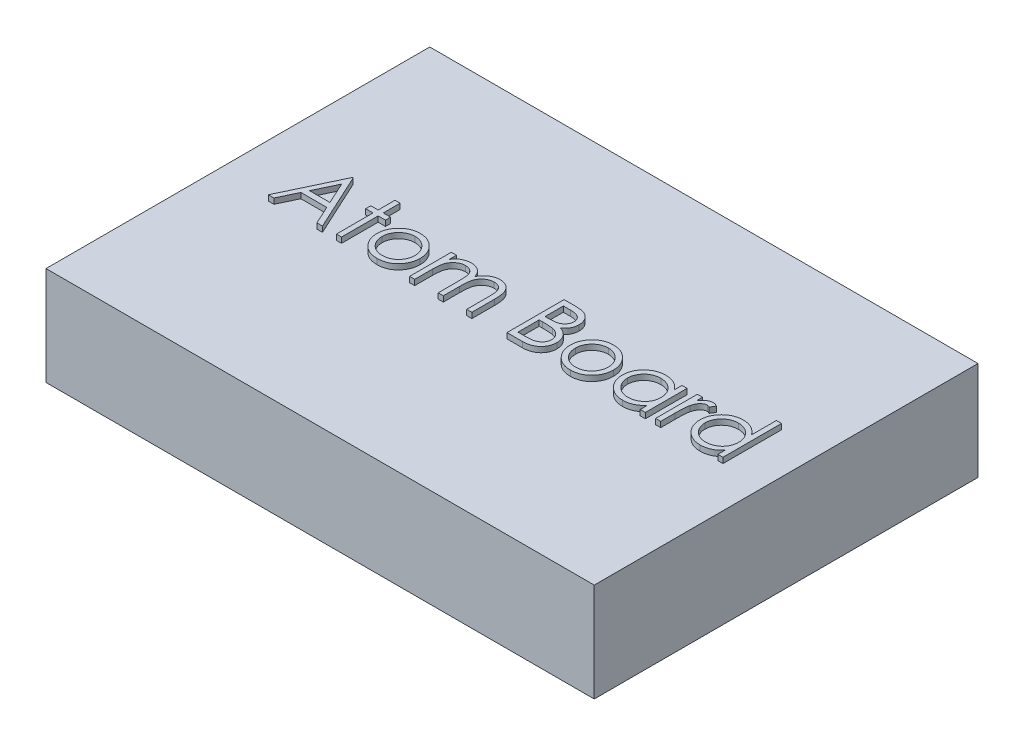
SolidWorks part; units mm, degrees
ref_plane "Front Plane" through (0, 0, 0) normal (0, 0, 1) x (1, 0, 0)
ref_plane "Top Plane" through (0, 0, 0) normal (0, 1, 0) x (1, 0, 0)
ref_plane "Right Plane" through (0, 0, 0) normal (1, 0, 0) x (0, 0, -1)
sketch "Sketch1" plane through (0, 0, 0) normal (0, 1, 0) x (1, 0, 0)
  line L1 (-127, -88.9) -> (127, -88.9)
  line L2 (-127, -88.9) -> (-127, 88.9)
  line L3 (-127, 88.9) -> (127, 88.9)
  line L4 (127, -88.9) -> (127, 88.9)
  line L5 (-127, -88.9) -> (127, 88.9) construction
  line L6 (-127, 88.9) -> (127, -88.9) construction
  point P0 (0, 0)
  dimension "D1" = 254
  dimension "D2" = 177.8
extrude "Boss-Extrude1" add sketch "Sketch1" along normal blind 45.72
sketch "Sketch2" plane through (0, 45.72, 0) normal (0, 1, 0) x (1, 0, 0)
  text T0 "Atom Board" font "Century Gothic" height in points 100
extrude "Boss-Extrude2" add sketch "Sketch2" along normal blind 2.54
sketch "Sketch3" plane through (0, 0, 0) normal (0, -1, 0) x (1, 0, 0)
  line L0 (0, 88.9) -> (0, -88.9) construction
  line L1 (-127, 88.9) -> (127, 88.9) construction
  line L2 (127, -88.9) -> (-127, -88.9) construction
  line L3 (127, 0) -> (-127, 0) construction
  line L4 (127, 88.9) -> (127, -88.9) construction
  line L5 (-127, -88.9) -> (-127, 88.9) construction
